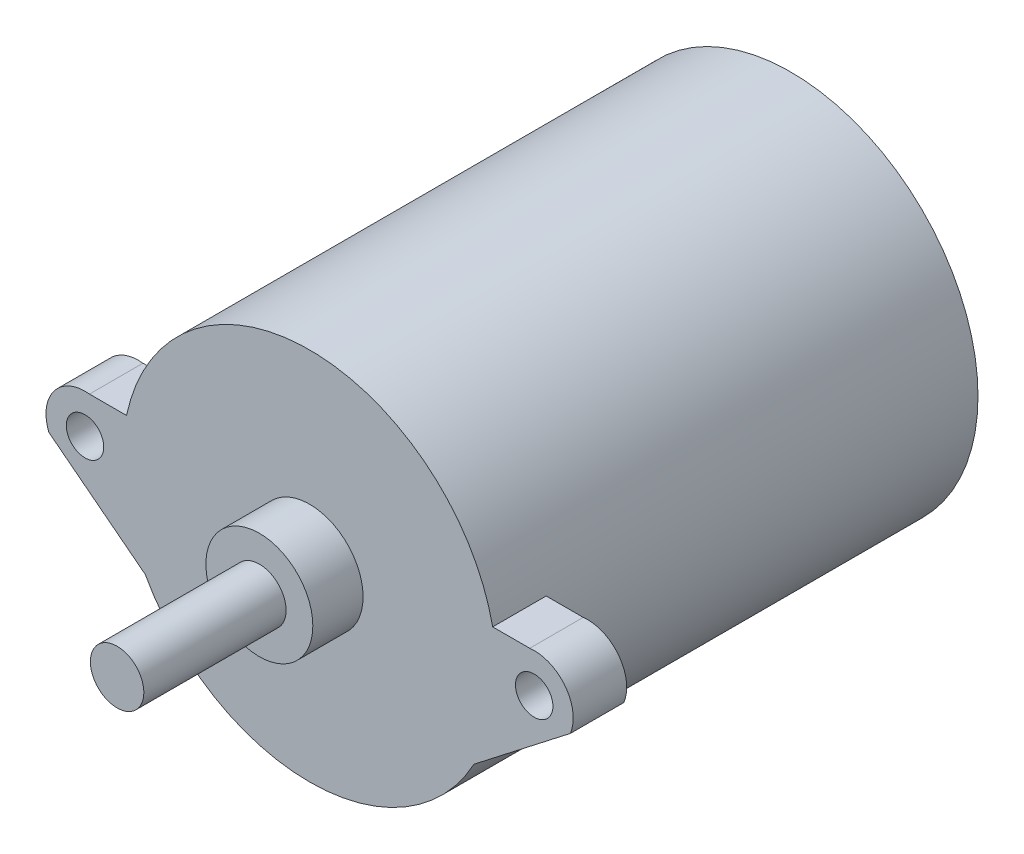
SolidWorks part; units mm, degrees
ref_plane "Front Plane" through (0, 0, 0) normal (0, 0, 1) x (1, 0, 0)
ref_plane "Top Plane" through (0, 0, 0) normal (0, 1, 0) x (1, 0, 0)
ref_plane "Right Plane" through (0, 0, 0) normal (1, 0, 0) x (0, 0, -1)
ref_plane "Plane1" through (0, 0, 33.02) normal (0, 0, 1) x (1, 0, 0)
sketch "Sketch1" plane through (0, 0, 33.02) normal (0, 0, 1) x (1, 0, 0)
  circle A0 centre (0, 0) radius 17.5
  dimension "D1" = 35
extrude "Boss-Extrude1" add sketch "Sketch1" against normal blind 45
ref_plane "Plane2" through (0, 0, 2.2098) normal (0, 0, -1) x (-1, 0, 0)
sketch "Sketch6" plane through (0, 0, 0) normal (0, 1, 0) x (1, 0, 0)
  line L0 (5, -33.02) -> (0, -33.02)
  line L1 (0, -33.02) -> (0, -51.02)
  line L2 (0, -51.02) -> (2.5, -51.02)
  line L3 (2.5, -51.02) -> (2.5, -37.72)
  line L4 (2.5, -37.72) -> (5, -37.72)
  line L5 (5, -37.72) -> (5, -33.02)
  line L6 (0, -33.02) -> (0, -51.02) construction
  line L7 (-55, -33.02) -> (55, -33.02) construction
  line L9 (-17.5, -33.02) -> (17.5, -33.02) construction
  dimension "D1" = 18
  dimension "D2" = 4.7
  dimension "D3" = 5
  dimension "D6" = 2.5
revolve "Revolve5" add sketch "Sketch6" angle 360 about L6
sketch "Sketch7" plane through (0, 0, 33.02) normal (0, 0, 1) x (1, 0, 0)
  line L0 (17.1202, 3.6262) -> (20.5839, 3.6262)
  line L1 (15.3665, -8.3738) -> (24.3816, -1.3738)
  line L2 (17.1202, 3.6262) -> (15.3665, -8.3738)
  line L3 (-17.1202, 3.6262) -> (-20.5839, 3.6262)
  line L4 (-15.3665, -8.3738) -> (-24.3816, -1.3738)
  line L5 (-17.1202, 3.6262) -> (-15.3665, -8.3738)
  circle A0 centre (21, 0) radius 1.75
  circle A1 centre (-21, 0) radius 1.75
  circle A2 centre (0, 0) radius 17.5 construction
  arc A3 (-20.5839, 3.6262) -> (-24.3816, -1.3738) centre (-21, 0) ccw
  arc A4 (20.5839, 3.6262) -> (24.3816, -1.3738) centre (21, 0) cw
  dimension "D1" = 3.5
  dimension "D2" = 21
  dimension "D3" = 42
  dimension "D4" = 3.65
  dimension "D5" = 12
  dimension "D6" = 5
extrude "Boss-Extrude2" add sketch "Sketch7" against normal blind 5
